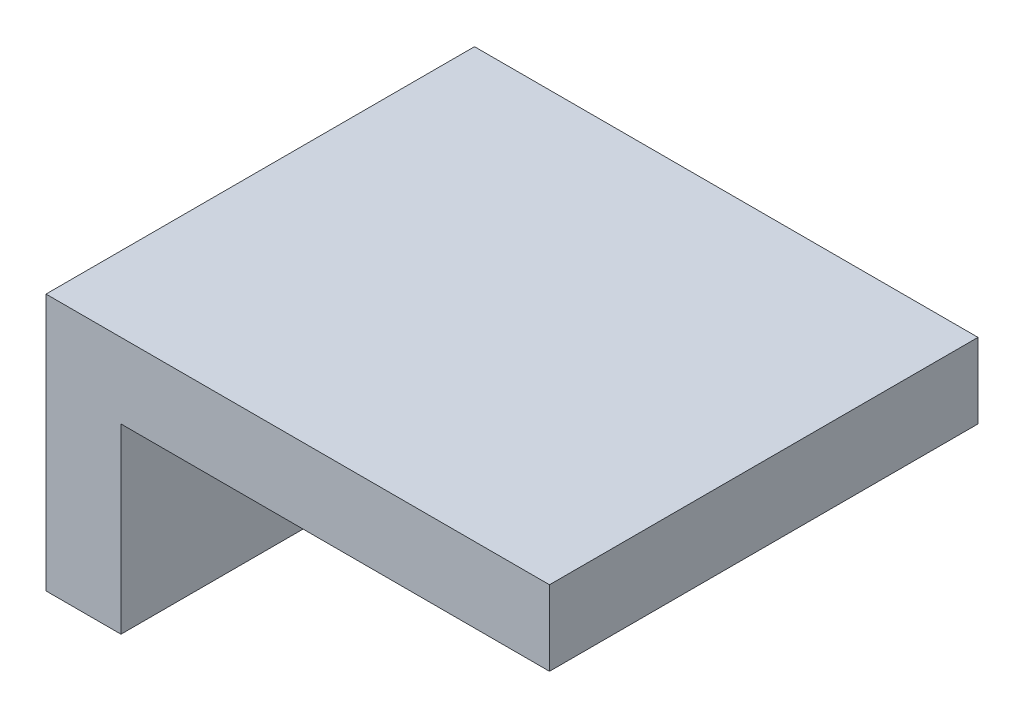
SolidWorks part; units mm, degrees
ref_plane "Front Plane" through (0, 0, 0) normal (0, 0, 1) x (1, 0, 0)
ref_plane "Top Plane" through (0, 0, 0) normal (0, 1, 0) x (1, 0, 0)
ref_plane "Right Plane" through (0, 0, 0) normal (1, 0, 0) x (0, 0, -1)
sketch "Sketch1" plane through (0, 0, 0) normal (1, 0, 0) x (0, 0, -1)
  line L1 (-20, -12) -> (20, -12)
  line L2 (-20, -12) -> (-20, 12)
  line L3 (-20, 12) -> (20, 12)
  line L4 (20, -12) -> (20, 12)
  line L5 (-20, -12) -> (20, 12) construction
  line L6 (-20, 12) -> (20, -12) construction
  point P0 (0, 0)
  dimension "D1" = 24
  dimension "D2" = 40
extrude "Boss-Extrude1" add sketch "Sketch1" along normal blind 7
sketch "Sketch2" plane through (7, 0, 0) normal (1, 0, 0) x (0, 0, -1)
  line L0 (20, -12) -> (20, 12) construction
  line L1 (-20, 12) -> (20, 12)
  line L2 (-20, 12) -> (-20, 5)
  line L3 (-20, 5) -> (20, 5)
  line L4 (20, 12) -> (20, 5)
  dimension "D1" = 7
extrude "Boss-Extrude2" add sketch "Sketch2" along normal blind 40
sketch "Sketch3" plane through (0, 0, 0) normal (-1, 0, 0) x (0, 0, 1)
  line L0 (0, -13.2) -> (0, 13.2) construction
  circle A0 centre (-10.0489, 0) radius 2.5
  circle A1 centre (10.0489, 0) radius 2.5
  dimension "D1" = 5
extrude "Cut-Extrude1" cut sketch "Sketch3" against normal blind 14
